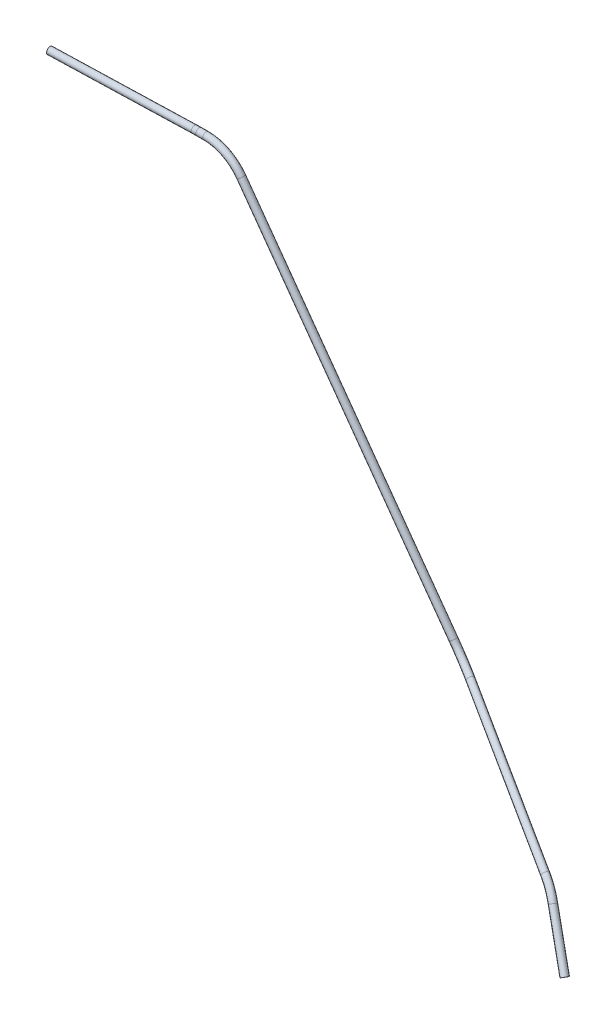
SolidWorks part; units mm, degrees
ref_plane "Płaszczyzna XY" through (0, 0, 0) normal (0, 0, 1) x (1, 0, 0)
ref_plane "Płaszczyzna XZ" through (0, 0, 0) normal (0, 1, 0) x (1, 0, 0)
ref_plane "Płaszczyzna YZ" through (0, 0, 0) normal (1, 0, 0) x (0, 0, -1)
sketch3d "Szkic 3D1"
  line L0 (101.0022, -599.7552, 230.4125) -> (74.8507, -559.1165, 215.5461)
  line L4 (-307.5272, -187.948, 132.2582) -> (-111.816, -478.1491, 124.407)
  line L5 (-88.3741, -496.7236, 131.3101) -> (59.5045, -546.8674, 207.3409)
  line L6 (-340.6942, -170.3141, 132.7353) -> (-347.4551, -170.3141, 132.7353)
  line L7 (-351.9187, -170.1763, 132.9437) -> (-478.785, -162.3231, 144.8295)
  arc A0 (59.5045, -546.8674, 207.3409) -> (74.8507, -559.1165, 215.5461) centre (50.2023, -579.1496, 204.1429) ccw
  arc A2 (-307.5272, -187.948, 132.2582) -> (-340.6942, -170.3141, 132.7353) centre (-340.6942, -210.2994, 131.6535) ccw
  arc A4 (-347.4551, -170.3141, 132.7353) -> (-351.9187, -170.1763, 132.9437) centre (-347.4551, -148.2635, 166.1085) ccw
  arc A5 (-111.816, -478.1491, 124.407) -> (-88.3741, -496.7236, 131.3101) centre (-86.0221, -461.4461, 150.0018) ccw
  point P8 (-319.4196, -170.3141, 132.7353)
  point P11 (-340.6942, -211.3812, 171.6389)
  point P15 (69.0514, -550.1046, 212.2493)
  point P17 (65.2579, -580.4989, 173.9699)
  point P20 (-102.5255, -491.925, 124.0343)
  point P21 (-106.8624, -476.3318, 180.7184)
  point P22 (-349.6939, -170.3141, 132.7353)
  point P24 (-347.4551, -114.8903, 144.058)
  dimension "D1" = 40
ref_plane "Płaszczyzna1" through (101.0022, -599.7552, 230.4125) normal (-0.5172, 0.8038, -0.294) x (0.8534, 0.5104, -0.1059)
sketch "Szkic1" plane through (101.0022, -599.7552, 230.4125) normal (-0.5172, 0.8038, -0.294) x (0.8534, 0.5104, -0.1059)
  circle A0 centre (0, 0) radius 3.25
  circle A1 centre (0, 0) radius 1.75
  dimension "D1" = 6.5
  dimension "D2" = 3.5
sweep "Wyciągnięcie po ścieżce4" add profiles "Szkic1" path "Szkic 3D1"
